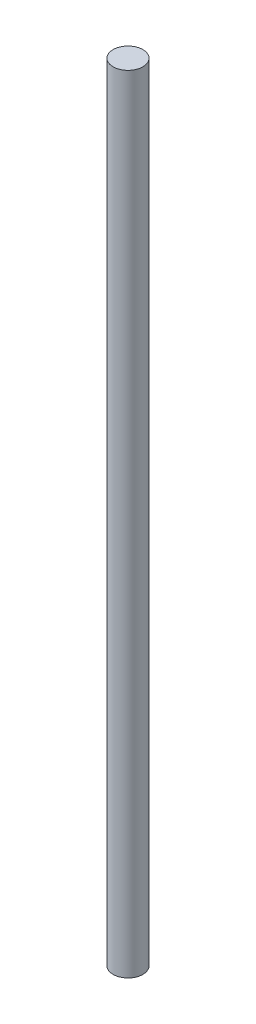
SolidWorks part; units mm, degrees
ref_plane "Front Plane" through (0, 0, 0) normal (0, 0, 1) x (1, 0, 0)
ref_plane "Top Plane" through (0, 0, 0) normal (0, 1, 0) x (1, 0, 0)
ref_plane "Right Plane" through (0, 0, 0) normal (1, 0, 0) x (0, 0, -1)
sketch "Sketch1" plane through (0, 0, 0) normal (0, 1, 0) x (1, 0, 0)
  circle A0 centre (0, 0) radius 5.5
extrude "Boss-Extrude1" add sketch "Sketch1" along normal blind 290
